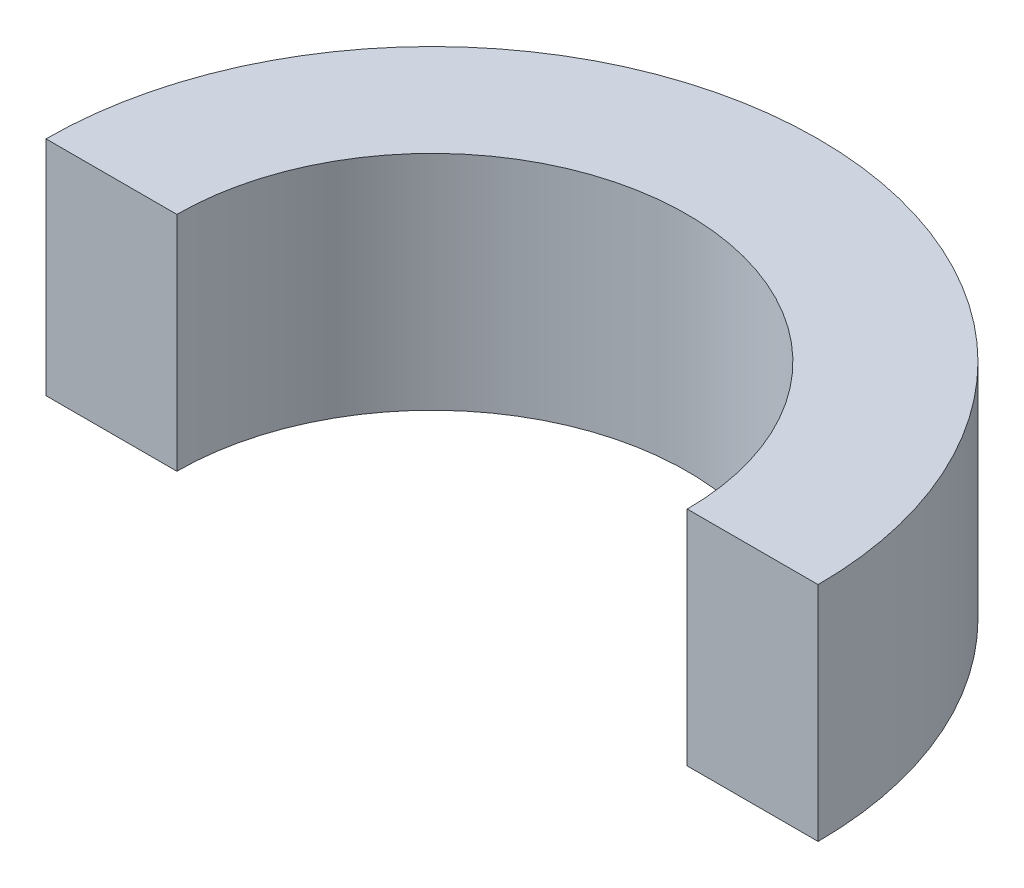
SolidWorks part; units mm, degrees
ref_plane "Front Plane" through (0, 0, 0) normal (0, 0, 1) x (1, 0, 0)
ref_plane "Top Plane" through (0, 0, 0) normal (0, 1, 0) x (1, 0, 0)
ref_plane "Right Plane" through (0, 0, 0) normal (1, 0, 0) x (0, 0, -1)
sketch "Sketch2" plane through (0, 0, 0) normal (0, 1, 0) x (1, 0, 0)
  line L0 (-19.5, 0) -> (-29.5, 0)
  line L1 (19.5, 0) -> (29.5, 0)
  arc A0 (19.5, 0) -> (-19.5, 0) centre (0, 0) ccw
  arc A1 (-29.5, 0) -> (29.5, 0) centre (0, 0) cw
  dimension "D1" = 10
  dimension "D2" = 10
extrude "Boss-Extrude1" add sketch "Sketch2" along normal blind 17 contours A1 L0 A0 L1
